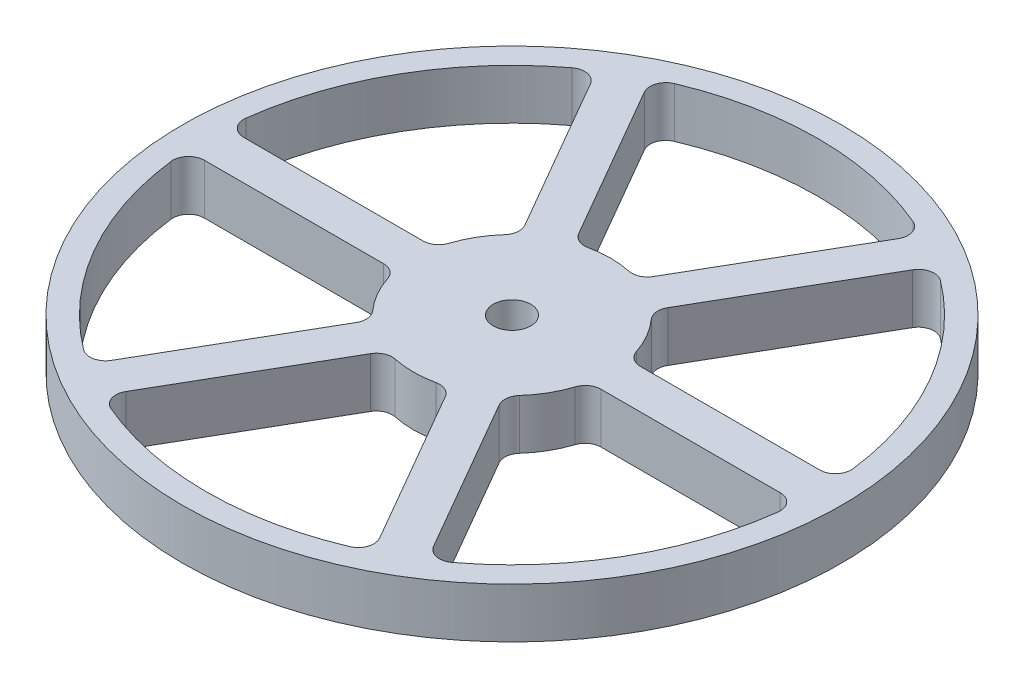
SolidWorks part; units mm, degrees
material "6061-T6 (SS)"
ref_plane "Front Plane" through (0, 0, 0) normal (0, 0, 1) x (1, 0, 0)
ref_plane "Top Plane" through (0, 0, 0) normal (0, 1, 0) x (1, 0, 0)
ref_plane "Right Plane" through (0, 0, 0) normal (1, 0, 0) x (0, 0, -1)
sketch "Sketch2" plane through (0, 0, 0) normal (1, 0, 0) x (0, 0, -1)
  line L0 (0, 0) -> (-82.55, 0)
  line L1 (-82.55, 0) -> (-82.55, 12.7)
  line L2 (-82.55, 12.7) -> (0, 12.7)
  line L5 (0, 12.7) -> (0, 0)
  dimension "D1" = 82.55
  dimension "D2" = 12.7
ref_axis "Axis1" through (0, -0.75, 0) along (0, 1, 0)
revolve "Revolve1" add sketch "Sketch2" angle 360 about axis through (0, -0.75, 0) along (0, 1, 0)
sketch "Sketch8" plane through (0, 12.7, 0) normal (0, 1, 0) x (1, 0, 0)
  line L4 (0, 0) -> (0, 93.9995) construction
  line L5 (0, 0) -> (113.8372, 0) construction
  line L6 (-7.9173, 23.7132) -> (-34.3642, 69.5205)
  line L7 (7.9173, 23.7132) -> (34.3642, 69.5205)
  line L8 (0, 0) -> (-35, 60.6218) construction
  arc A0 (-7.9173, 23.7132) -> (7.9173, 23.7132) centre (0, 0) cw
  arc A1 (-34.3642, 69.5205) -> (34.3642, 69.5205) centre (0, 0) cw
  circle A2 centre (0, 0) radius 82.55 construction
  dimension "D1" = 25
  dimension "D2" = 5
  dimension "D3" = 5
  dimension "D4" = 30
extrude "Cut-Extrude1" cut sketch "Sketch8" against normal through all
fillet "Fillet1" radius 4 4 edges at (7.9173, 6.35, -23.7132) (34.3642, 6.35, -69.5205) (-7.9173, 6.35, -23.7132) (-34.3642, 6.35, -69.5205)
pattern_circular "CirPattern4" count 6 over 360 about axis through (0, 0, 0) along (0, 1, 0) of "Cut-Extrude1", "Fillet1"
chamfer "Chamfer2" distance 1 angle 45 1 edges at (0, 0, -82.55)
hole_wizard "3/8 (0.375) Diameter Hole1" positions "Sketch9" profile "Sketch11" hole size "3/8" standard "ANSI Inch" end condition through all
sketch "Sketch9" plane through (0, 0, 0) normal (0, -1, 0) x (-1, 0, 0)
  point P0 (0, 0)
sketch "Sketch11" plane through (0, 0, 0) normal (1, 0, 0) x (0, 0, -1)
  line L0 (0, 0) -> (0, 12.7)
  line L1 (0, 12.7) -> (4.7625, 12.7)
  line L2 (4.7625, 12.7) -> (4.7625, 0)
  line L5 (4.7625, 0) -> (0, 0)
  line L11 (0, -6.35) -> (0, 107.95) construction
  dimension "Thru Hole Dia." = 9.525
  dimension "Thru Hole Depth" = 12.7
sketch "Sketch12" plane through (0, 12.7, 0) normal (0, 1, 0) x (1, 0, 0)
  circle A0 centre (0, 0) radius 82.55
  circle A1 centre (0, 0) radius 83.55
  circle A2 centre (0, 0) radius 82.55 construction
  dimension "D1" = 1
extrude "Boss-Extrude1" add sketch "Sketch12" against normal blind 12.7
equation "\"TubeDiameter\" = 6.500in"
equation "\"D1@Sketch2\"=\"TubeDiameter\"/2"
